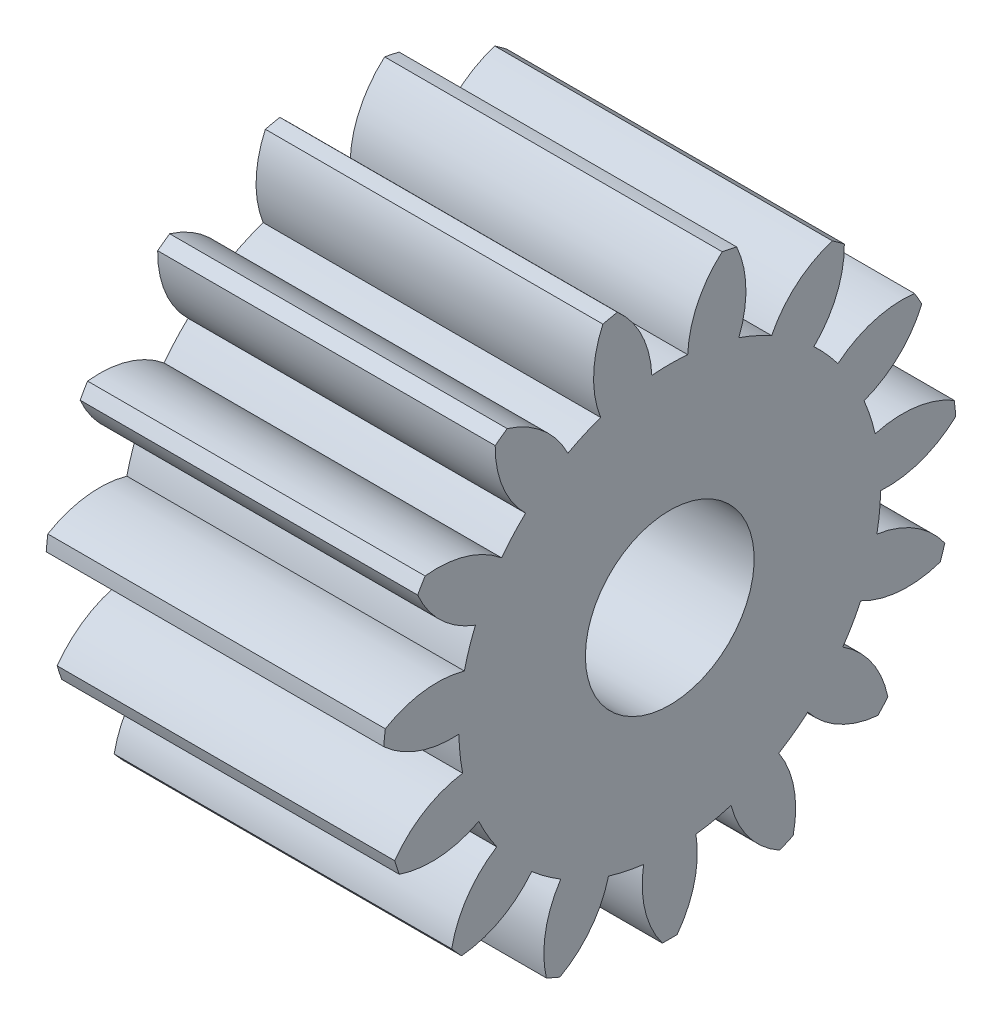
SolidWorks part; units mm, degrees
ref_plane "Plane1" through (0, 0, 0) normal (0, 0, 1) x (1, 0, 0)
ref_plane "Plane2" through (0, 0, 0) normal (0, 1, 0) x (1, 0, 0)
ref_plane "Plane3" through (0, 0, 0) normal (1, 0, 0) x (0, 0, -1)
sketch "HoldingSke" plane through (0, 0, 0) normal (0, 1, 0) x (1, 0, 0)
  line L0 (0, 0) -> (0.9659, -0.2588)
  line L1 (-15, 0) -> (100, 0) construction
  line L2 (0, 0) -> (-2.1039, 2.3779)
  line L3 (0, 0) -> (-11.863, 4.5341)
  line L4 (0, 0) -> (8.3417, 2.2352)
  line L5 (0, 0) -> (-46.8476, -17.4728)
  line L6 (0, 0) -> (-8.2896, -5.593)
  line L7 (-2.1039, 2.3779) -> (8.6586, 51.2059)
  line L8 (-76.2, 54.61) -> (-75.3, 54.61)
  line L9 (-71.009, 38.7566) -> (-53.1078, 45.2721)
  line L10 (-76.2, 71.12) -> (104.1128, 71.12)
  line L11 (0, 0) -> (-10, 0)
  line L12 (-76.2, 101.6) -> (-76.162, 101.6)
  line L13 (24.9733, 27.94) -> (52.9518, 28.4284)
  line L14 (24.9733, 27.94) -> (24.9743, 27.94)
  line L15 (24.9733, 27.94) -> (100.4006, 29.5858)
  line L16 (-63.627, -1) -> (-12.827, -1)
  circle A0 centre (0, 0) radius 2.5
  circle A1 centre (0, 0) radius 6.249
  circle A2 centre (0, 0) radius 37.5
  circle A3 centre (0, 0) radius 2.5
  dimension "MHD" = 12.498
  dimension "Hub_dia" = 75
  dimension "Bore" = 5
  dimension "MBD" = 5
  dimension "Num_teeth" = 15
  dimension "Pitch" = 1
  dimension "Overall_len" = 50
  dimension "Show_teeth" = 15
  dimension "Thickness" = 10
  dimension "OAL" = 50.0001
  dimension "T_dim" = 0.9
  dimension "Ap" = 20
  dimension "H" = 19.05
  dimension "Pitch_radius" = 180.3128
  dimension "Width" = 10
  dimension "Backlash" = 0.038
  dimension "Addendum_fac" = 1
  dimension "Dedendum_fac" = 1.25
  dimension "Clearance_fac" = 0.25
  dimension "Dedendum_add" = 0.001
  dimension "Module" = 1
sketch "BasProSke" plane through (0, 0, 0) normal (0, 1, 0) x (1, 0, 0)
  line L0 (-10, 0) -> (60, 0) construction
  line L1 (0, 0) -> (0, 8.5)
  line L2 (0, 0) -> (10, 0)
  line L3 (10, 0) -> (10, 8.5)
  line L4 (10, 8.5) -> (0, 8.5)
  dimension "Thickness" = 10
  dimension "Diameter" = 17
revolve "Base-Revolve" add sketch "BasProSke" angle 360 about L0
sketch "TooCutSke" plane through (0, 0, 0) normal (1, 0, 0) x (0, 0, -1)
  line L1 (0, 0) -> (0, 107) construction
  line L2 (0, 0) -> (-0.8504, 7.4516) construction
  line L3 (0, 0) -> (-3.1044, 14.6049) construction
  line L4 (-0.8504, 7.4516) -> (-1.5522, 7.3025) construction
  arc A0 (0.5316, 6.2263) -> (-0.5316, 6.2263) centre (0, 0) ccw
  arc A1 (1.5766, 8.3784) -> (-1.5766, 8.3784) centre (0, 0) ccw
  circle A2 centre (0, 0) radius 7.5 construction
  circle A3 centre (0, 0) radius 7.0477 construction
  arc A4 (-0.5316, 6.2263) -> (-1.5766, 8.3784) centre (-3.5289, 6.1005) ccw
  arc A5 (1.5766, 8.3784) -> (0.5316, 6.2263) centre (3.5289, 6.1005) ccw
  dimension "Root_dia" = 12.498
  dimension "Overcut_dia" = 17.0508
  dimension "Pitch_dia" = 15
  dimension "Base_dia" = 14.0954
  dimension "Flank_rad" = 3
  dimension "Half_ang" = 12
  dimension "Half_CT" = 0.7175
extrude "ToothCut" cut sketch "TooCutSke" along normal through all
fillet "Breaks" [suppressed] radius 0.02
fillet "RootFillets" [suppressed] radius 0.251
pattern_circular "TeethCuts" count 15 every 24 about axis through (-10, 0, 0) along (1, 0, 0) of "ToothCut", "RootFillets", "Breaks"
sketch "HubNeaOneSke" plane through (0, 0, 0) normal (-1, 0, 0) x (0, 0, 1)
  circle A0 centre (0, 0) radius 6.249
  dimension "Diameter" = 12.498
extrude "HubNearOne" [suppressed] add sketch "HubNeaOneSke" along normal blind 40.0001
sketch "HubNeaBotSke" plane through (0, 0, 0) normal (-1, 0, 0) x (0, 0, 1)
  circle A0 centre (0, 0) radius 6.249
  dimension "Diameter" = 12.498
extrude "HubNearBoth" [suppressed] add sketch "HubNeaBotSke" along normal blind 20
ref_plane "FarPln" through (10, 0, 0) normal (1, 0, 0) x (0, 0, -1)
sketch "HubFarSke" plane through (10, 0, 0) normal (1, 0, 0) x (0, 0, -1)
  circle A0 centre (0, 0) radius 6.249
  dimension "Diameter" = 12.498
extrude "HubFar" [suppressed] add sketch "HubFarSke" along normal blind 20
sketch "BorSke" plane through (0, 0, 0) normal (1, 0, 0) x (0, 0, -1)
  circle A0 centre (0, 0) radius 2.5
  dimension "Diameter" = 5
extrude "Bore" cut sketch "BorSke" along normal mid plane 100.0001
sketch "KeySke" plane through (0, 0, 0) normal (1, 0, 0) x (0, 0, -1)
  line L0 (-1, 0) -> (-1, 3.4)
  line L1 (-1, 3.4) -> (1, 3.4)
  line L2 (1, 3.4) -> (1, 0)
  line L3 (0, 0) -> (0, 34) construction
  line L4 (-1, 0) -> (1, 0)
  dimension "Offset" = 3.4
  dimension "Width" = 2
extrude "Keyway" [suppressed] cut sketch "KeySke" along normal mid plane 100.0001
pattern_circular "Keyway2" [suppressed] count 2 every 90 about axis through (-10, 0, 0) along (1, 0, 0)
equation "' \"Module@HoldingSke\" = 6.35"
equation "' \"Num_teeth@HoldingSke\" = 12"
equation "' \"Ap@HoldingSke\" =  20"
equation "' \"Ap@HoldingSke\" = 20"
equation "' \"Width@HoldingSke\" = 0.5 * 25.4"
equation "' \"Hub_dia@HoldingSke\"= 1 * 25.4"
equation "' \"Hub_dia@HoldingSke\" = 1 * 25.4"
equation "' \"Overall_len@HoldingSke\" = 1.0 * 25.4"
equation "' \"Bore@HoldingSke\" = 0.75 * 25.4"
equation "' \"T_dim@HoldingSke\" = 0.1 * 25.4"
equation "' \"Width@KeySke\" = 0.25 * 25.4"
equation "' \"Show_teeth@HoldingSke\" = 13"
equation "' \"Backlash@HoldingSke\" = 0.009 * 25.4"
equation "' \"Addendum_fac@HoldingSke\" = 1.0"
equation "' \"Dedendum_fac@HoldingSke\" = 1.25"
equation "' \"Dedendum_add@HoldingSke\" = 0.00005 * 25.4"
equation "' \"Clearance_fac@HoldingSke\" = 0.25"
equation "\"Pitch@HoldingSke\" = 1 / \"Module@HoldingSke\""
equation "\"Overcut_dia@TooCutSke\" = (\"Num_teeth@HoldingSke\" + 2 * \"Addendum_fac@HoldingSke\") / \"Pitch@HoldingSke\" + 0.002 * 25.4"
equation "\"Pitch_dia@TooCutSke\" = \"Num_teeth@HoldingSke\" / \"Pitch@HoldingSke\""
equation "\"Base_dia@TooCutSke\" = \"Num_teeth@HoldingSke\" / \"Pitch@HoldingSke\" * cos((\"Ap@HoldingSke\"  * 3.14159265 / 180))"
equation "\"Root_dia@TooCutSke\" = (\"Num_teeth@HoldingSke\" + 2) / \"Pitch@HoldingSke\" - 2 * (\"Addendum_fac@HoldingSke\" + \"Dedendum_fac@HoldingSke\") / \"Pitch@HoldingSke\" - \"Dedendum_add@HoldingSke\" * 2"
equation "\"Half_ang@TooCutSke\" = 180 / \"Num_teeth@HoldingSke\""
equation "\"Half_CT@TooCutSke\" = \"Num_teeth@HoldingSke\" / \"Pitch@HoldingSke\" * sin((3.14159265 / 2 / \"Num_teeth@HoldingSke\")) / 2 - 7 * \"Backlash@HoldingSke\" / 4"
equation "\"Flank_rad@TooCutSke\" = \"Num_teeth@HoldingSke\" / \"Pitch@HoldingSke\" / 5"
equation "\"Radius@RootFillets\" = \"Clearance_fac@HoldingSke\" / \"Pitch@HoldingSke\" + \"Dedendum_add@HoldingSke\""
equation "\"Break_rad@Breaks\" = 0.02 / \"Pitch@HoldingSke\""
equation "\"Thickness@HoldingSke\" = \"Width@HoldingSke\""
equation "\"OAL@HoldingSke\" = \"Thickness@HoldingSke\""
equation "\"MHD@HoldingSke\" = (\"Num_teeth@HoldingSke\" + 2) / \"Pitch@HoldingSke\" - 2 * (\"Addendum_fac@HoldingSke\" + \"Dedendum_fac@HoldingSke\")  / \"Pitch@HoldingSke\" - \"Dedendum_add@HoldingSke\" * 2"
equation "\"MBD@HoldingSke\" = (\"Num_teeth@HoldingSke\" + 2) / \"Pitch@HoldingSke\" - 2 * (\"Addendum_fac@HoldingSke\" + \"Dedendum_fac@HoldingSke\")  / \"Pitch@HoldingSke\" - \"Dedendum_add@HoldingSke\" * 2 - 0.002 * 25.4"
equation "\"MHD@HoldingSke\" = ((sgn( \"MHD@HoldingSke\" - \"Hub_dia@HoldingSke\" )-1)*( \"MHD@HoldingSke\" - \"Hub_dia@HoldingSke\" ))/-2+ \"Hub_dia@HoldingSke\""
equation "\"MBD@HoldingSke\" = ((sgn( \"MBD@HoldingSke\" - \"Bore@HoldingSke\" )-1)*( \"MBD@HoldingSke\" - \"Bore@HoldingSke\" ))/-2+ \"Bore@HoldingSke\""
equation "\"OAL@HoldingSke\" = ((sgn( \"OAL@HoldingSke\" - \"Overall_len@HoldingSke\" )+1)*( \"OAL@HoldingSke\" - \"Overall_len@HoldingSke\" ))/2 + \"Overall_len@HoldingSke\" + 0.000002 * 25.4"
equation "\"Num_teeth@TeethCuts\" = int( \"Show_teeth@HoldingSke\" ) + 1"
equation "\"Num_teeth@TeethCuts\" = ((sgn( \"Num_teeth@TeethCuts\" - \"Num_teeth@HoldingSke\" )-1)*( \"Num_teeth@TeethCuts\" - \"Num_teeth@HoldingSke\" ))/-2+ \"Num_teeth@HoldingSke\""
equation "\"Num_teeth@TeethCuts\" = ((sgn( \"Num_teeth@TeethCuts\" - 2.0)+1)*( \"Num_teeth@TeethCuts\" - 2.0))/2 +2.0"
equation "\"Angle@TeethCuts\" = 360.0 / \"Num_teeth@HoldingSke\""
equation "\"Diameter@BasProSke\" = (\"Num_teeth@HoldingSke\" + 2 * \"Addendum_fac@HoldingSke\") / \"Pitch@HoldingSke\""
equation "\"Thickness@BasProSke\"  = \"Thickness@HoldingSke\""
equation "' \"Fillet_rad@BasProSke\" =  \"Thickness@HoldingSke\" * 0.05"
equation "' \"Fillet_rad@BasProSke\" = \"Thickness@HoldingSke\" * 0.05"
equation "\"MHD@HoldingSke\" = ((sgn( \"MHD@HoldingSke\" - \"Root_dia@TooCutSke\" )-1)*( \"MHD@HoldingSke\" - \"Root_dia@TooCutSke\" ))/-2+ \"Root_dia@TooCutSke\""
equation "\"Diameter@HubNeaOneSke\" = \"MHD@HoldingSke\""
equation "\"Length@HubNearOne\" = \"OAL@HoldingSke\" - \"Thickness@BasProSke\""
equation "\"Diameter@HubNeaBotSke\" = \"MHD@HoldingSke\""
equation "\"Length@HubNearBoth\" = ( \"OAL@HoldingSke\" - \"Thickness@BasProSke\" ) / 2.0"
equation "\"Thickness@FarPln\" = \"Thickness@BasProSke\""
equation "\"Diameter@HubFarSke\" = \"MHD@HoldingSke\""
equation "\"Length@HubFar\" = ( \"OAL@HoldingSke\" - \"Thickness@BasProSke\" ) / 2.0"
equation "\"Diameter@BorSke\" = \"MBD@HoldingSke\""
equation "\"D1@Bore\" = \"OAL@HoldingSke\" * 2.0"
equation "\"D1@Keyway\" = \"OAL@HoldingSke\" * 2.0"
equation "\"Offset@KeySke\" = \"T_dim@HoldingSke\" + \"MBD@HoldingSke\" / 2.0"
